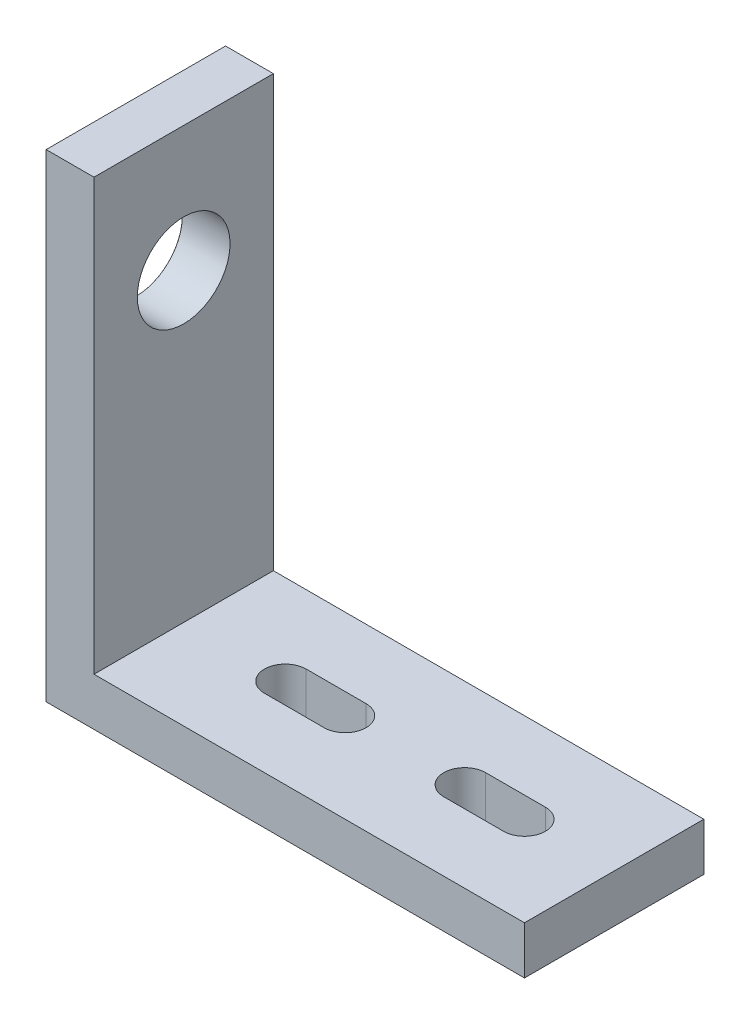
SolidWorks part; units mm, degrees
ref_plane "前视基准面" through (0, 0, 0) normal (0, 0, 1) x (1, 0, 0)
ref_plane "上视基准面" through (0, 0, 0) normal (0, 1, 0) x (1, 0, 0)
ref_plane "右视基准面" through (0, 0, 0) normal (1, 0, 0) x (0, 0, -1)
sketch "草图1" plane through (0, 0, 0) normal (0, 0, 1) x (1, 0, 0)
  line L0 (0, 80) -> (0, 0)
  line L1 (0, 0) -> (80, 0)
  line L2 (8, 80) -> (8, 8)
  line L3 (8, 8) -> (80, 8)
  line L4 (0, 80) -> (8, 80)
  line L5 (80, 8) -> (80, 0)
  dimension "D2" = 80
  dimension "D3" = 80
  dimension "D1" = 8
extrude "凸台-拉伸1" add sketch "草图1" along normal blind 30
sketch "草图2" plane through (0, 8, 0) normal (0, 1, 0) x (1, 0, 0)
  line L0 (80, -15) -> (72.5104, -15) construction
  line L1 (80, -30) -> (80, 0) construction
  line L3 (55, -15) -> (65, -15) construction
  line L4 (55, -11.5) -> (65, -11.5)
  line L5 (55, -18.5) -> (65, -18.5)
  line L7 (25, -15) -> (35, -15) construction
  line L8 (25, -11.5) -> (35, -11.5)
  line L9 (25, -18.5) -> (35, -18.5)
  arc A0 (55, -11.5) -> (55, -18.5) centre (55, -15) ccw
  arc A1 (65, -18.5) -> (65, -11.5) centre (65, -15) ccw
  arc A2 (25, -11.5) -> (25, -18.5) centre (25, -15) ccw
  arc A3 (35, -18.5) -> (35, -11.5) centre (35, -15) ccw
  point P8 (60, -15)
  point P16 (30, -15)
  dimension "D4" = 2
  dimension "D1" = 20
  dimension "D2" = 7
  dimension "D3" = 10
  dimension "D5" = 30
extrude "切除-拉伸1" cut sketch "草图2" against normal blind 60
hole_wizard "Ø15.5 (15.5) 直径槽口1" positions "草图3" profile "草图4" size "Ø15.5" standard "GB" slot yes
sketch "草图3" plane through (0, 0, 0) normal (-1, 0, 0) x (0, 0, 1)
  line L0 (30, 80) -> (0, 80) construction
  line L1 (0, 80) -> (0, 0) construction
  point P0 (15, 59)
  dimension "D1" = 21
  dimension "D2" = 15
sketch "草图4" plane through (0, 59, 15) normal (0, 1, 0) x (0, 0, 1)
  line L0 (0, 0) -> (0, 21.6567)
  line L1 (0, 21.6567) -> (7.75, 17)
  line L2 (7.75, 17) -> (7.75, 0.025)
  line L3 (7.75, 0.025) -> (7.775, 0)
  line L5 (7.775, 0) -> (0, 0)
  line L6 (-7.75, 0.025) -> (-7.775, 0) construction
  line L10 (0, 21.6567) -> (-7.75, 17) construction
  line L11 (0, -6.35) -> (0, 107.95) construction
  dimension "孔直径" = 15.5
  dimension "孔深度" = 17
  dimension "近端锥形沉头孔直径" = 15.55
  dimension "近端锥形沉头孔角度" = 90
  dimension "导头角度" = 118
